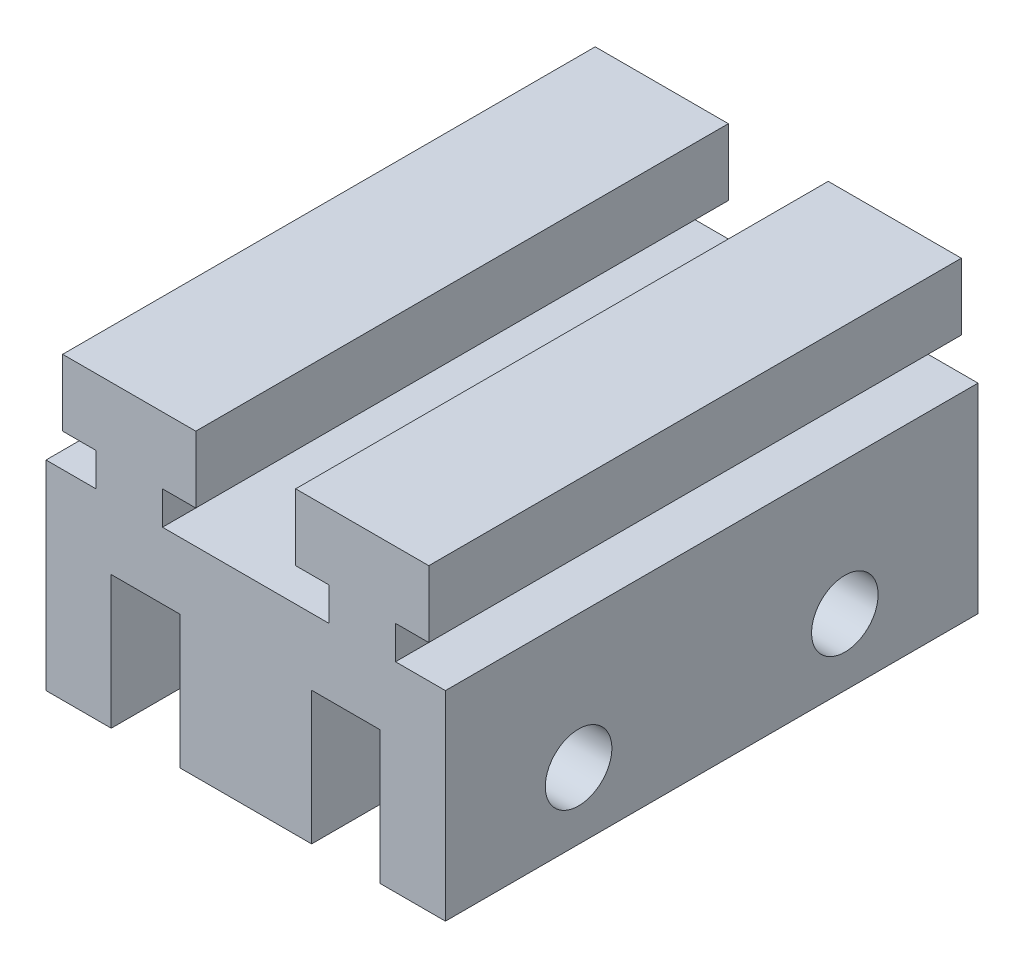
SolidWorks part; units mm, degrees
ref_plane "Front Plane" through (0, 0, 0) normal (0, 0, 1) x (1, 0, 0)
ref_plane "Top Plane" through (0, 0, 0) normal (0, 1, 0) x (1, 0, 0)
ref_plane "Right Plane" through (0, 0, 0) normal (1, 0, 0) x (0, 0, -1)
sketch "Sketch2" plane through (0, 0, 0) normal (0, 1, 0) x (1, 0, 0)
  line L0 (-4.95, 20) -> (4.95, 20)
  line L1 (-15, 20) -> (-10.1, 20)
  line L2 (-15, 20) -> (-15, -20)
  line L3 (-15, -20) -> (-10.1, -20)
  line L4 (-10.1, 20) -> (-10.1, -20)
  line L5 (10.1, 20) -> (15, 20)
  line L6 (10.1, 20) -> (10.1, -20)
  line L7 (10.1, -20) -> (15, -20)
  line L8 (15, 20) -> (15, -20)
  line L9 (-4.95, 20) -> (-4.95, -20)
  line L10 (-4.95, -20) -> (4.95, -20)
  line L11 (4.95, 20) -> (4.95, -20)
  point P8 (-10.1, 0)
  point P10 (10.1, 0)
  point P15 (-4.95, 0)
  point P16 (0, -20)
  dimension "D1" = 40
  dimension "D2" = 5.15
  dimension "D3" = 4.9
  dimension "D4" = 5.15
  dimension "D5" = 9.9
extrude "Boss-Extrude1" add sketch "Sketch2" along normal blind 10
sketch "Sketch3" plane through (-15, 0, 0) normal (-1, 0, 0) x (0, 0, 1)
  line L0 (-20, 0) -> (20, 0) construction
  circle A0 centre (-10, 5) radius 2.5
  circle A1 centre (10, 5) radius 2.5
  dimension "D3" = 5
  dimension "D1" = 10
  dimension "D2" = 10
  dimension "D4" = 5
extrude "Cut-Extrude1" cut sketch "Sketch3" against normal up to surface (30 mm away) up to face at (15, 5, 0)
sketch "Sketch4" plane through (0, 10, 0) normal (0, 1, 0) x (1, 0, 0)
  line L1 (-15, 20) -> (15, 20)
  line L2 (-15, 20) -> (-15, -20)
  line L3 (-15, -20) -> (15, -20)
  line L4 (15, 20) -> (15, -20)
extrude "Boss-Extrude2" add sketch "Sketch4" along normal blind 5
sketch "Sketch5" plane through (0, 0, 20) normal (0, 0, 1) x (1, 0, 0)
  line L0 (-11.25, 15) -> (-11.25, 17.5)
  line L1 (-15, 15) -> (15, 15) construction
  line L2 (-11.25, 17.5) -> (-13.75, 17.5)
  line L3 (-13.75, 17.5) -> (-13.75, 22.5)
  line L4 (-13.75, 22.5) -> (-3.75, 22.5)
  line L5 (-3.75, 22.5) -> (-3.75, 17.5)
  line L6 (-3.75, 17.5) -> (-6.25, 17.5)
  line L7 (-6.25, 17.5) -> (-6.25, 15)
  line L8 (-6.25, 15) -> (-11.25, 15)
  point P4 (0, 15)
  point P11 (-8.75, 15)
  dimension "D1" = 2.5
  dimension "D2" = 5
  dimension "D3" = 5
  dimension "D4" = 2.5
  dimension "D5" = 8.75
extrude "Boss-Extrude3" add sketch "Sketch5" against normal up to surface (40 mm away) up to face at (0, 5.8333, -20)
mirror "Mirror1" of "Boss-Extrude3"
